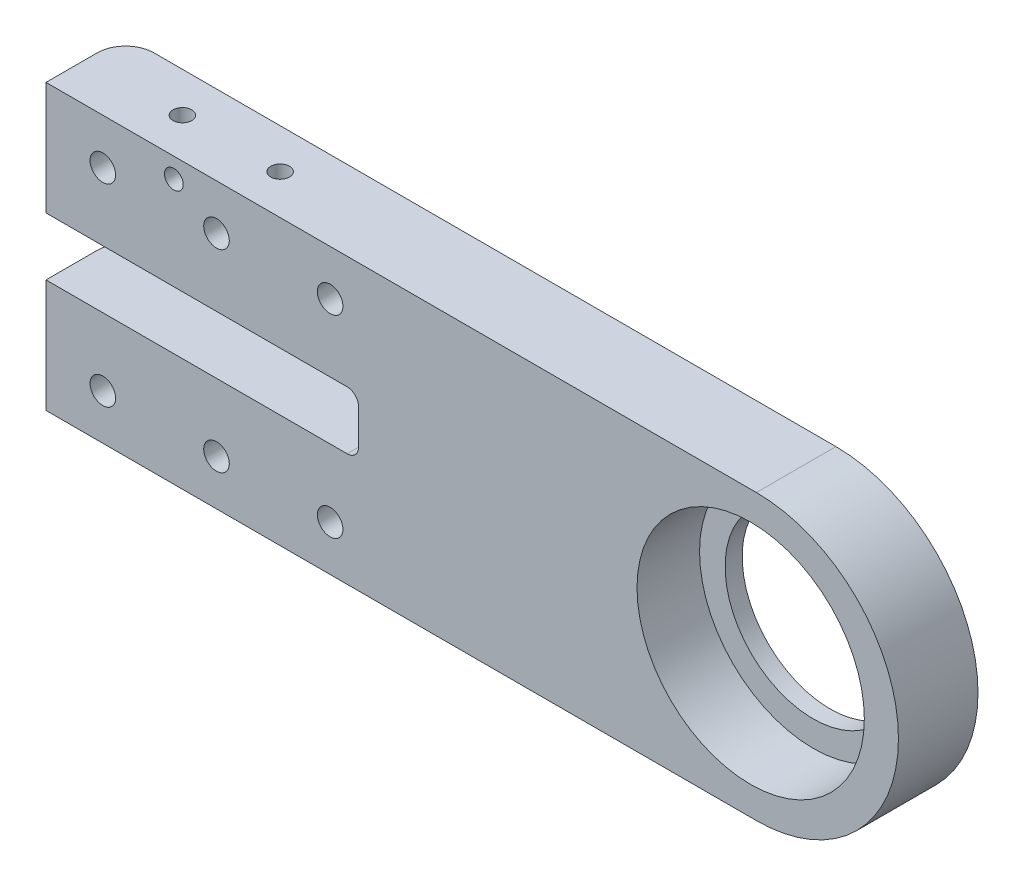
SolidWorks part; units mm, degrees
ref_plane "Front Plane" through (0, 0, 0) normal (0, 0, 1) x (1, 0, 0)
ref_plane "Top Plane" through (0, 0, 0) normal (0, 1, 0) x (1, 0, 0)
ref_plane "Right Plane" through (0, 0, 0) normal (1, 0, 0) x (0, 0, -1)
ref_plane "Plane1" through (0, 0, 0) normal (0, 0, -1) x (-1, 0, 0)
sketch "Sketch1" plane through (0, 0, 0) normal (0, 0, -1) x (-1, 0, 0)
  line L0 (-125, -50) -> (0, -50)
  line L1 (0, -50) -> (0, 0)
  line L2 (0, 0) -> (-125, 0)
  arc A0 (-125, 0) -> (-125, -50) centre (-125, -25) ccw
extrude "Boss-Extrude1" add sketch "Sketch1" against normal blind 14
sketch "Sketch2" plane through (0, 0, 14) normal (0, 0, 1) x (1, 0, 0)
  line L0 (0, -30.1) -> (55, -30.1)
  line L1 (55, -30.1) -> (55, -19.9)
  line L2 (55, -19.9) -> (0, -19.9)
  line L3 (0, -19.9) -> (0, -30.1)
extrude "Cut-Extrude1" cut sketch "Sketch2" against normal through all
hole_wizard "#8 Clearance Hole1" positions "Sketch4" profile "Sketch3" hole size "#8" standard "ANSI Inch"
sketch "Sketch4" plane through (0, 0, 0) normal (0, 0, -1) x (-1, 0, 0)
  point P0 (-10, -8)
  point P1 (-10, -42)
  point P2 (-30, -42)
  point P3 (-30, -8)
  point P4 (-50, -8)
  point P5 (-50, -42)
sketch "Sketch3" plane through (10, -8, 0) normal (1, 0, 0) x (0, 1, 0)
  line L0 (0, 0) -> (0, 14)
  line L1 (0, 14) -> (2.25, 14)
  line L2 (2.25, 14) -> (2.25, 0)
  line L5 (2.25, 0) -> (0, 0)
  line L11 (0, -6.35) -> (0, 107.95) construction
  dimension "Thru Hole Dia." = 4.5
  dimension "Thru Hole Depth" = 14
hole_wizard "#4 Clearance Hole1" positions "Sketch6" profile "Sketch5" hole size "#4" standard "ANSI Inch"
sketch "Sketch6" plane through (0, 0, 14) normal (0, 0, 1) x (1, 0, 0)
  point P0 (22.5, -3.5)
sketch "Sketch5" plane through (22.5, -3.5, 14) normal (1, 0, 0) x (0, -1, 0)
  line L0 (0, 0) -> (0, 14)
  line L1 (0, 14) -> (1.65, 14)
  line L2 (1.65, 14) -> (1.65, 0)
  line L5 (1.65, 0) -> (0, 0)
  line L11 (0, -6.35) -> (0, 107.95) construction
  dimension "Thru Hole Dia." = 3.3
  dimension "Thru Hole Depth" = 14
hole_wizard "#4 Clearance Hole2" positions "Sketch8" profile "Sketch7" hole size "#4" standard "ANSI Inch"
sketch "Sketch8" plane through (0, 0, 0) normal (0, 1, 0) x (1, 0, 0)
  point P0 (17, -7)
  point P1 (34.2, -7)
sketch "Sketch7" plane through (17, 0, 7) normal (1, 0, 0) x (0, 0, 1)
  line L0 (0, 0) -> (0, 19.9)
  line L1 (0, 19.9) -> (1.65, 19.9)
  line L2 (1.65, 19.9) -> (1.65, 0)
  line L5 (1.65, 0) -> (0, 0)
  line L11 (0, -6.35) -> (0, 107.95) construction
  dimension "Thru Hole Dia." = 3.3
  dimension "Thru Hole Depth" = 19.9
hole_wizard "Hole1" positions "Sketch10" profile "Sketch9" legacy
sketch "Sketch10" plane through (0, 0, 14) normal (0, 0, 1) x (1, 0, 0)
  point P0 (124, -25)
sketch "Sketch9" plane through (124, -25, 14) normal (1, 0, 0) x (0, -1, 0)
  line L0 (0, 0) -> (0, 14)
  line L1 (0, 14) -> (15.5, 14)
  line L2 (15.5, 14) -> (15.5, 11)
  line L3 (15.5, 11) -> (20, 11)
  line L4 (20, 11) -> (20, 0)
  line L5 (20, 0) -> (0, 0)
  line L6 (0, 110) -> (0, -10) construction
  dimension "Diameter" = 31
  dimension "Depth" = 14
  dimension "C-Bore Diameter" = 40
  dimension "C-Bore Depth" = 11
chamfer "Chamfer1" distance 2.45 angle 45 6 edges at (27.75, -42, 0) (7.75, -42, 0) (47.75, -42, 0) (27.75, -8, 0) (7.75, -8, 0) (47.75, -8, 0)
fillet "Fillet1" radius 2 2 edges at (55, -19.9, 7) (55, -30.1, 7)
fillet "Fillet2" radius 5 2 edges at (0, -40.05, 0) (0, -9.95, 0)
